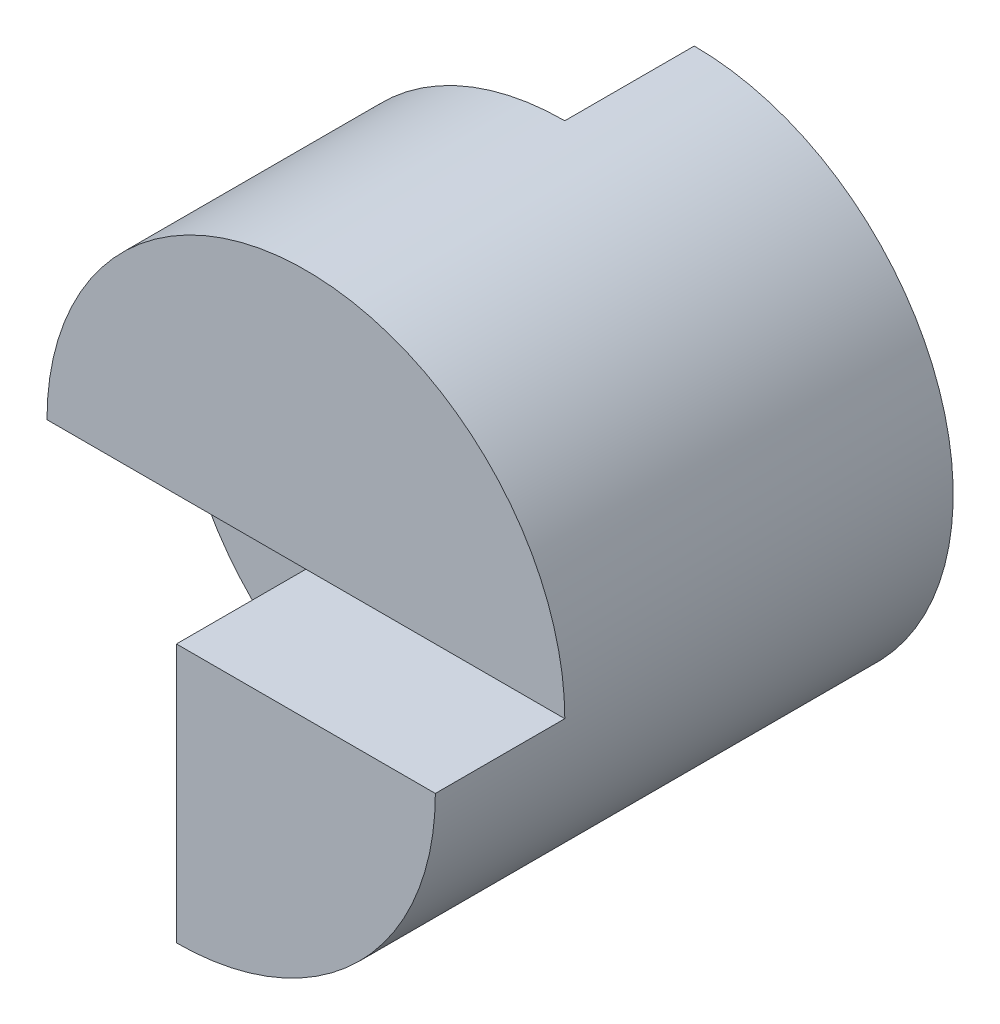
SolidWorks part; units mm, degrees
ref_plane "Front Plane" through (0, 0, 0) normal (0, 0, 1) x (1, 0, 0)
ref_plane "Top Plane" through (0, 0, 0) normal (0, 1, 0) x (1, 0, 0)
ref_plane "Right Plane" through (0, 0, 0) normal (1, 0, 0) x (0, 0, -1)
sketch "Sketch1" plane through (0, 0, 0) normal (0, 0, 1) x (1, 0, 0)
  circle A0 centre (0, 0) radius 20
  dimension "D1" = 40
extrude "Boss-Extrude1" add sketch "Sketch1" along normal blind 40
sketch "Sketch2" plane through (0, 0, 0) normal (0, 1, 0) x (1, 0, 0)
  line L1 (-20, -40) -> (0, -40)
  line L2 (-20, -40) -> (-20, -30)
  line L3 (-20, -30) -> (0, -30)
  line L4 (0, -40) -> (0, -30)
  line L5 (-20, 0) -> (0, 0)
  line L6 (-20, 0) -> (-20, -10)
  line L7 (-20, -10) -> (0, -10)
  line L8 (0, 0) -> (0, -10)
  dimension "D1" = 10
  dimension "D2" = 10
  dimension "D3" = 20
  dimension "D4" = 20
extrude "Cut-Extrude1" cut sketch "Sketch2" along normal blind 40
sketch "Sketch3" plane through (0, 0, 40) normal (0, 0, 1) x (1, 0, 0)
  line L0 (0, 20) -> (0, 0) construction
  line L1 (0, 20) -> (0, 0)
  line L2 (0, 0) -> (20, 0)
  arc A0 (20, 0) -> (0, 20) centre (0, 0) ccw
  arc A1 (-20, 0) -> (0, 20) centre (0, 0) ccw construction
extrude "Cut-Extrude2" cut sketch "Sketch3" against normal blind 10
sketch "Sketch4" plane through (0, 0, 40) normal (0, 0, 1) x (1, 0, 0)
  line L0 (-20, 0) -> (20, 0) construction
  line L1 (-20, 0) -> (0, 0)
  line L2 (0, 0) -> (0, -20)
  arc A0 (0, -20) -> (-20, 0) centre (0, 0) cw
  arc A1 (-20, 0) -> (20, 0) centre (0, 0) ccw construction
extrude "Cut-Extrude3" cut sketch "Sketch4" against normal blind 20
sketch "Sketch5" plane through (0, 0, 0) normal (0, 1, 0) x (1, 0, 0)
  line L1 (-20, 0) -> (0, 0)
  line L2 (-20, 0) -> (-20, -10)
  line L3 (-20, -10) -> (0, -10)
  line L4 (0, 0) -> (0, -10)
extrude "Cut-Extrude4" cut sketch "Sketch5" against normal blind 20
